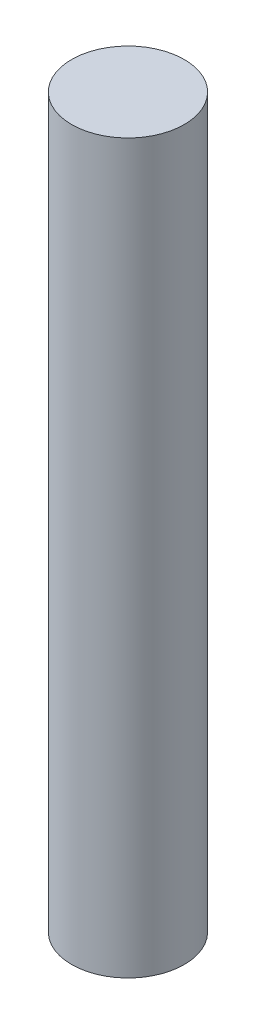
SolidWorks part; units mm, degrees
ref_plane "Front Plane" through (0, 0, 0) normal (0, 0, 1) x (1, 0, 0)
ref_plane "Top Plane" through (0, 0, 0) normal (0, 1, 0) x (1, 0, 0)
ref_plane "Right Plane" through (0, 0, 0) normal (1, 0, 0) x (0, 0, -1)
sketch "Sketch1" plane through (0, 0, 0) normal (0, 1, 0) x (1, 0, 0)
  circle A0 centre (-17.2623, 6.3895) radius 3.95
extrude "Boss-Extrude1" add sketch "Sketch1" along normal blind 51 contours A0
